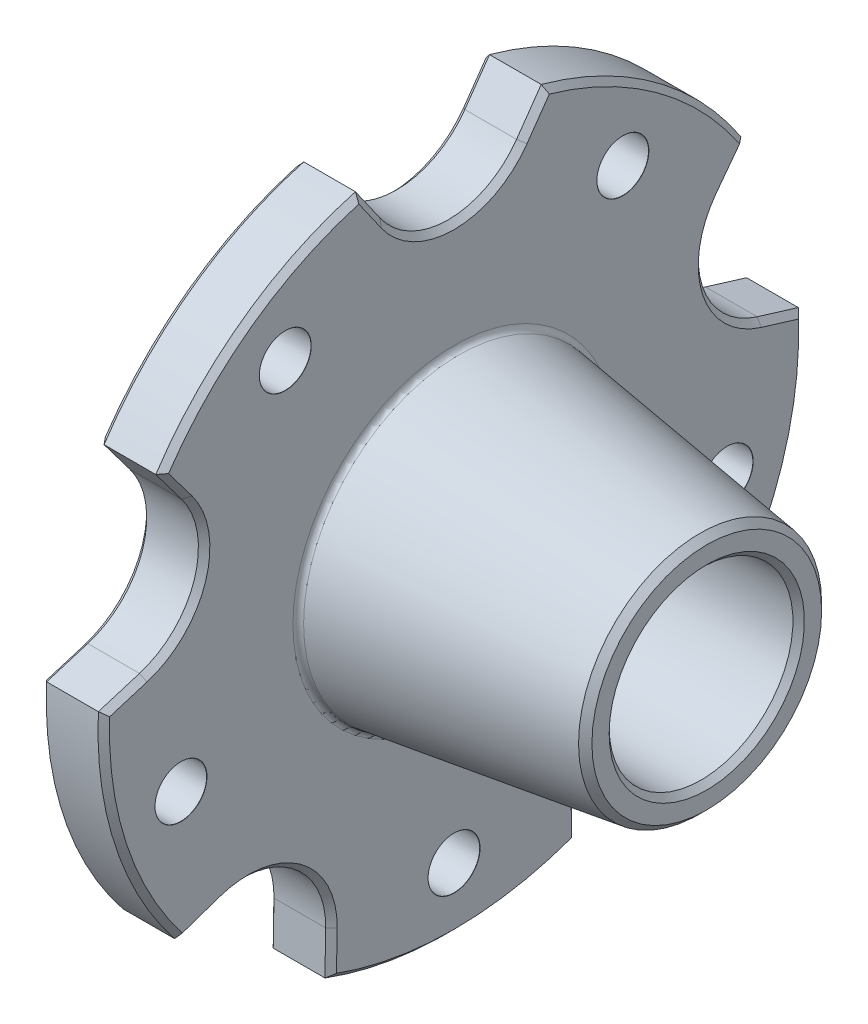
SolidWorks part; units mm, degrees
material "Plain Carbon Steel"
ref_plane "Front Plane" through (0, 0, 0) normal (0, 0, 1) x (1, 0, 0)
ref_plane "Top Plane" through (0, 0, 0) normal (0, 1, 0) x (1, 0, 0)
ref_plane "Right Plane" through (0, 0, 0) normal (1, 0, 0) x (0, 0, -1)
sketch "Sketch1" plane through (0, 0, 0) normal (0, 0, 1) x (1, 0, 0)
  line L0 (0, 12) -> (0, 25)
  line L1 (0, 25) -> (15, 25)
  line L2 (15, 25) -> (15, 61)
  line L3 (15, 61) -> (26, 61)
  line L4 (26, 61) -> (26, 27.1838)
  line L5 (26, 27.1838) -> (70, 21)
  line L6 (70, 21) -> (70, 16)
  line L7 (70, 16) -> (38, 16)
  line L8 (38, 16) -> (38, 8)
  line L9 (38, 8) -> (12, 8)
  line L10 (12, 8) -> (12, 12)
  line L11 (12, 12) -> (0, 12)
  line L12 (0, 0) -> (38, 0) construction
  dimension "D1" = 8
  dimension "D2" = 12
  dimension "D3" = 12
  dimension "D4" = 15
  dimension "D5" = 26
  dimension "D6" = 38
  dimension "D7" = 70
  dimension "D8" = 16
  dimension "D9" = 21
  dimension "D10" = 8
  dimension "D11" = 25
  dimension "D12" = 61
revolve "Revolve1" add sketch "Sketch1" angle 360 about L12
sketch "Sketch3" plane through (15, 0, 0) normal (-1, 0, 0) x (0, 0, 1)
  line L0 (0, 0) -> (0, 61) construction
  line L1 (-11.8777, 52.6831) -> (-16.1727, 58.817)
  line L2 (11.8777, 52.6831) -> (16.1727, 58.817)
  circle A0 centre (0, 0) radius 61 construction
  arc A1 (16.1727, 58.817) -> (-16.1727, 58.817) centre (0, 0) ccw
  arc A2 (-11.8777, 52.6831) -> (11.8777, 52.6831) centre (0, 61) ccw
  dimension "D1" = 29
  dimension "D2" = 35
  dimension "D3" = 70
extrude "Cut-Extrude2" cut sketch "Sketch3" against normal up to next
fillet "Fillet1" radius 1 4 edges at (38, 0, 16) (26, 0, 27.1838) (15, 0, 25) (12, 0, 12)
sketch "Sketch4" plane through (15, 0, 0) normal (-1, 0, 0) x (0, 0, 1)
  line L0 (0, 0) -> (0, 50) construction
  line L1 (0, 0) -> (-29.3893, 40.4508) construction
  circle A0 centre (0, 0) radius 50 construction
  dimension "D1" = 100
  dimension "D2" = 36
hole_wizard "M3 Clearance Hole2" positions "3DSketch2" profile "Sketch6" hole size "M3" standard "ISO" end condition up to next
sketch3d "3DSketch2"
  point P0 (15, 40.4508, -29.3893)
sketch "Sketch6" plane through (15, 40.4508, -29.3893) normal (0, 1, 0) x (0, 0, 1)
  line L0 (0, 0) -> (0, 11)
  line L1 (0, 11) -> (4.525, 11)
  line L2 (4.5, 10.975) -> (4.5, 0.025)
  line L3 (4.5, 0.025) -> (4.525, 0)
  line L5 (4.525, 0) -> (0, 0)
  line L6 (-4.5, 0.025) -> (-4.525, 0) construction
  line L7 (4.525, 11) -> (4.5, 10.975)
  line L8 (-4.525, 11) -> (-4.5, 10.975) construction
  line L11 (0, -6.35) -> (0, 107.95) construction
  dimension "Thru Hole Dia." = 9
  dimension "Thru Hole Depth" = 11
  dimension "Near C'Sink Dia." = 9.05
  dimension "Near C'Sink Angle" = 90
  dimension "Far C'Sink Dia." = 9.05
  dimension "Far C'Sink Angle" = 90
pattern_circular "CirPattern6" count 5 over 360 about axis through (0, 0, 0) along (1, 0, 0) of "Cut-Extrude2", "M3 Clearance Hole2"
chamfer "Chamfer2" distance 1 angle 45 46 edges at (12, 0, 8) (38, 0, 8) (70, 0, 16) (70, 0, 21) (26, 55.7501, 14.0252) (26, 55.7501, -14.0252) (26, 46.5, 0) (15, 55.7501, -14.0252) (15, 55.7501, 14.0252) (15, 46.5, 0) (26, 49.35, -35.8549) (26, 49.35, 35.8549) (15, 49.35, 35.8549) (15, 49.35, -35.8549) (0, 0, 12) (0, 0, 25) (15, 30.5665, 48.6875) (15, 3.889, 57.3555) (15, 14.3693, 44.2241) (26, 3.889, 57.3555) (26, 30.5665, 48.6875) (26, 14.3693, 44.2241) (26, 30.5665, -48.6875) (26, 3.889, -57.3555) (26, 14.3693, -44.2241) (15, 3.889, -57.3555) (15, 30.5665, -48.6875) (15, 14.3693, -44.2241) (26, -18.85, -58.0144) (15, -18.85, -58.0144) (26, -36.859, -44.1157) (26, -53.3466, -21.4225) (26, -37.6193, -27.332) (15, -53.3466, -21.4225) (15, -36.859, -44.1157) (15, -37.6193, -27.332) (26, -61, 0) (15, -61, 0) (15, -36.859, 44.1157) (15, -53.3466, 21.4225) (15, -37.6193, 27.332) (26, -53.3466, 21.4225) (26, -36.859, 44.1157) (26, -37.6193, 27.332) (26, -18.85, 58.0144) (15, -18.85, 58.0144)
